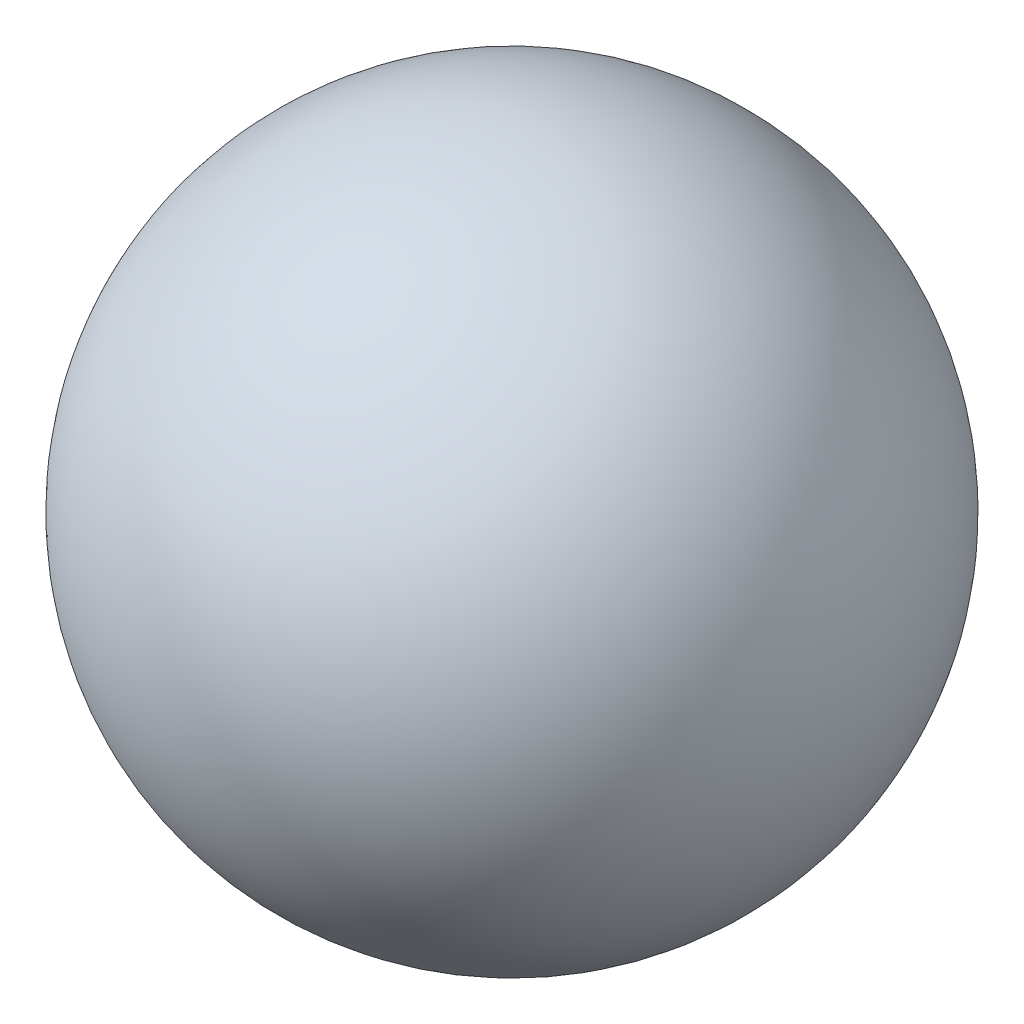
SolidWorks part; units mm, degrees
material "普通碳钢"
ref_plane "前视基准面" through (0, 0, 0) normal (0, 0, 1) x (1, 0, 0)
ref_plane "上视基准面" through (0, 0, 0) normal (0, 1, 0) x (1, 0, 0)
ref_plane "右视基准面" through (0, 0, 0) normal (1, 0, 0) x (0, 0, -1)
ref_plane "基准面1" through (0, 0, 0) normal (0, 0, 1) x (1, 0, 0)
sketch "草图1" plane through (0, 0, 0) normal (0, 0, 1) x (1, 0, 0)
  line L0 (3.6905, 9.75) -> (1.3095, 9.75)
  line L1 (3.6905, 9.75) -> (1.3095, 9.75) construction
  arc A0 (1.3095, 9.75) -> (3.6905, 9.75) centre (2.5, 9.75) cw
revolve "旋转1" add sketch "草图1" angle 360 about L1
